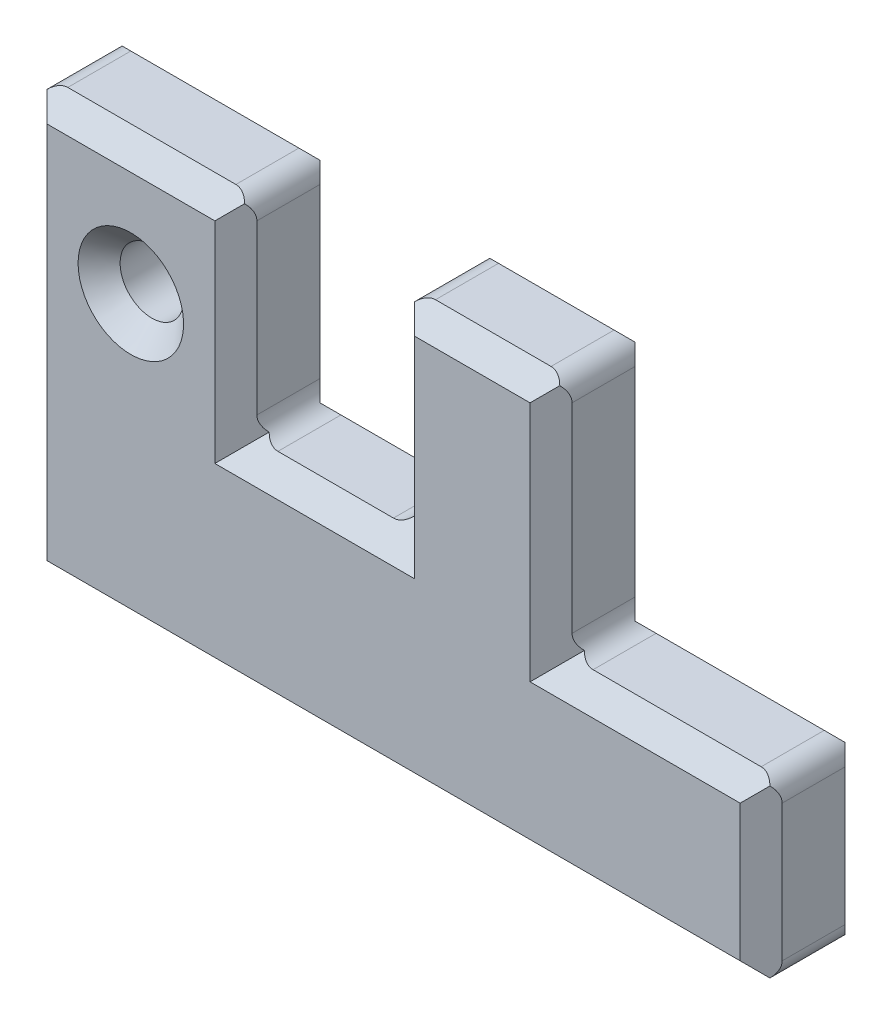
SolidWorks part; units mm, degrees
ref_plane "Front Plane" through (0, 0, 0) normal (0, 0, 1) x (1, 0, 0)
ref_plane "Top Plane" through (0, 0, 0) normal (0, 1, 0) x (1, 0, 0)
ref_plane "Right Plane" through (0, 0, 0) normal (1, 0, 0) x (0, 0, -1)
sketch "Sketch1" plane through (0, 0, 0) normal (0, 0, 1) x (1, 0, 0)
  line L0 (0, 0) -> (0, 2)
  line L1 (0, 2) -> (1, 2)
  line L2 (1, 2) -> (1, 1)
  line L3 (1, 1) -> (1.75, 1)
  line L4 (1.75, 1) -> (1.75, 2)
  line L5 (1.75, 2) -> (2.5, 2)
  line L6 (2.5, 2) -> (2.5, 0.85)
  line L7 (2.5, 0.85) -> (3.5, 0.85)
  line L8 (3.5, 0.85) -> (3.5, 0)
  line L9 (3.5, 0) -> (0, 0)
  dimension "D1" = 2
  dimension "D2" = 3.5
  dimension "D3" = 1
  dimension "D4" = 1.75
  dimension "D5" = 2.5
  dimension "D6" = 0.85
  dimension "D7" = 1
extrude "Boss-Extrude1" add sketch "Sketch1" along normal blind 0.5
chamfer "Chamfer1" distance 0.1 angle 45 20 edges at (3.5, 0.425, 0) (3, 0.85, 0) (2.5, 1.425, 0) (2.125, 2, 0) (1.75, 1.5, 0) (1.375, 1, 0) (1, 1.5, 0) (0.5, 2, 0) (0, 1, 0) (1.75, 0, 0) (0, 1, 0.5) (0.5, 2, 0.5) (1, 1.5, 0.5) (1.375, 1, 0.5) (1.75, 1.5, 0.5) (2.125, 2, 0.5) (2.5, 1.425, 0.5) (3, 0.85, 0.5) (3.5, 0.425, 0.5) (1.75, 0, 0.5)
fillet "Fillet4" radius 0.1 10 edges at (0, 0, 0.25) (3.5, 0, 0.25) (3.5, 0.85, 0.25) (2.5, 0.85, 0.25) (1.75, 1, 0.25) (1, 1, 0.25) (2.5, 2, 0.25) (1.75, 2, 0.25) (1, 2, 0.25) (0, 2, 0.25)
sketch "Sketch2" plane through (0, 0, 0.5) normal (0, 0, 1) x (1, 0, 0)
  line L0 (0.9, 1.9) -> (0.1, 1.9) construction
  circle A0 centre (0.5, 1.4) radius 0.151
  point P2 (0, 0)
  point P3 (0, 0)
  point P4 (0.4687, 1.4916)
  point P7 (0, 0)
  point P8 (0, 0)
  point P9 (0.385, 1.3974)
  point P10 (-0.8648, 2.1394)
  dimension "D1" = 0.5
extrude "Cut-Extrude1" cut sketch "Sketch2" against normal through all
chamfer "Chamfer2" distance 0.1 angle 45 1 edges at (0.651, 1.4, 0.5)
